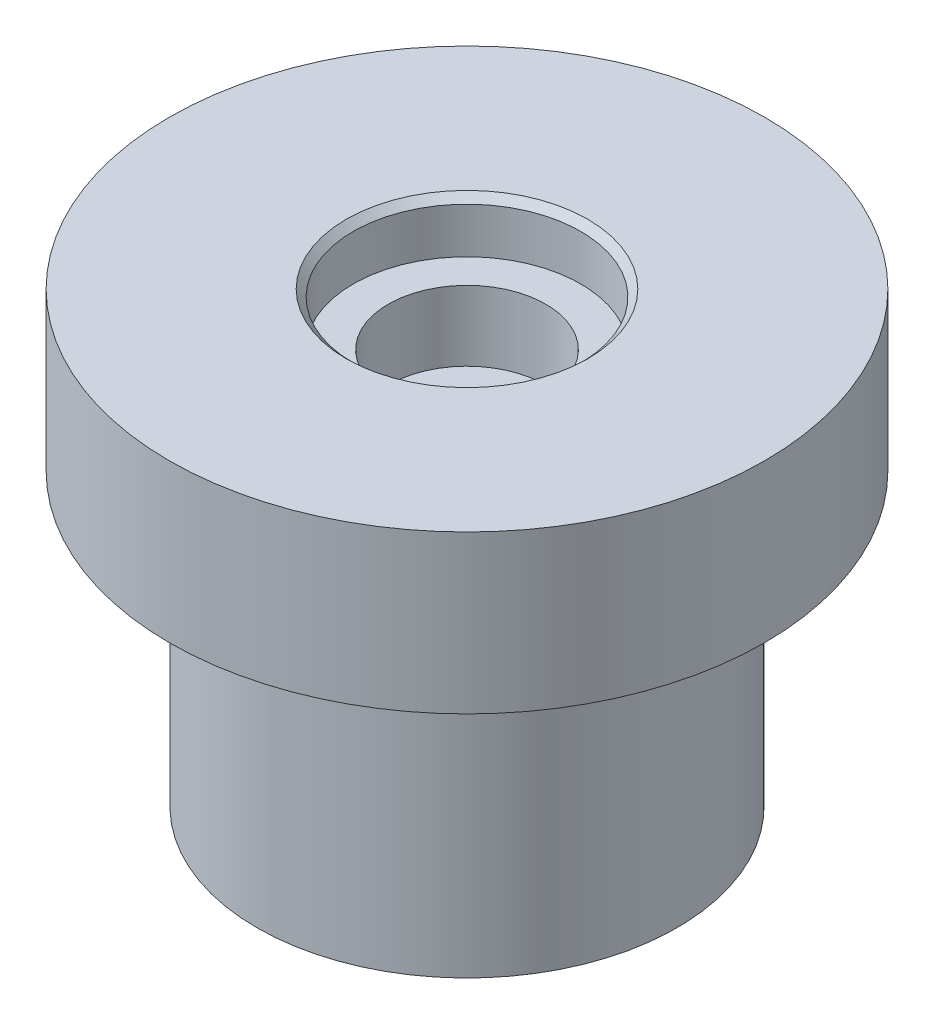
SolidWorks part; units mm, degrees
material "PBT (一般用)"
ref_plane "正面" through (0, 0, 0) normal (0, 0, 1) x (1, 0, 0)
ref_plane "平面" through (0, 0, 0) normal (0, 1, 0) x (1, 0, 0)
ref_plane "右側面" through (0, 0, 0) normal (1, 0, 0) x (0, 0, -1)
sketch "Sketch1" plane through (0, 0, 0) normal (0, 1, 0) x (1, 0, 0)
  circle A0 centre (0, 0) radius 7
extrude "Boss-Extrude1" add sketch "Sketch1" along normal blind 12.8
sketch "Sketch2" plane through (0, 0, 0) normal (0, -1, 0) x (1, 0, 0)
  circle A0 centre (0, 0) radius 6
extrude "Cut-Extrude1" cut sketch "Sketch2" against normal through all flip side to cut
sketch "Sketch3" plane through (0, 12.8, 0) normal (0, 1, 0) x (1, 0, 0)
  circle A0 centre (0, 0) radius 3.25
extrude "Cut-Extrude2" cut sketch "Sketch3" against normal blind 1.5
sketch "Sketch4" plane through (0, 11.3, 0) normal (0, 1, 0) x (1, 0, 0)
  circle A0 centre (0, 0) radius 2.25
extrude "Cut-Extrude3" cut sketch "Sketch4" against normal blind 2
chamfer "Chamfer1" distance 0.2 angle 45 1 edges at (0, 12.8, 3.25)
sketch "ｽｹｯﾁ1" plane through (0, 12.8, 0) normal (0, 1, 0) x (1, 0, 0)
  circle A0 centre (0, 0) radius 8.5
  circle A1 centre (0, 0) radius 5.2124
extrude "ﾎﾞｽ - 押し出し1" add sketch "ｽｹｯﾁ1" against normal blind 4.5
